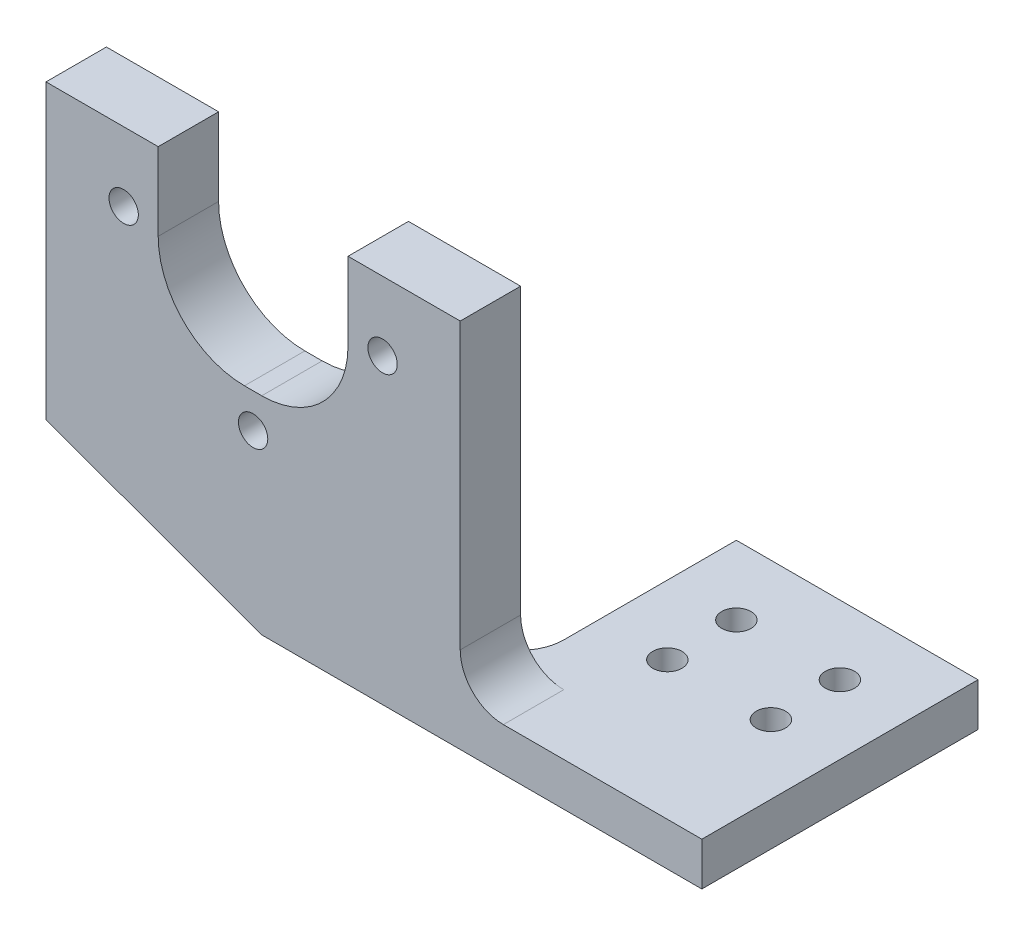
SolidWorks part; units mm, degrees
ref_plane "Front Plane" through (0, 0, 0) normal (0, 0, 1) x (1, 0, 0)
ref_plane "Top Plane" through (0, 0, 0) normal (0, 1, 0) x (1, 0, 0)
ref_plane "Right Plane" through (0, 0, 0) normal (1, 0, 0) x (0, 0, -1)
sketch "Sketch1" plane through (0, 0, 0) normal (0, 1, 0) x (1, 0, 0)
  line L1 (-14, -16) -> (14, -16)
  line L2 (-14, -16) -> (-14, 16)
  line L3 (-14, 16) -> (14, 16)
  line L4 (14, -16) -> (14, 16)
  line L5 (-14, -16) -> (14, 16) construction
  line L6 (-14, 16) -> (14, -16) construction
  point P0 (0, 0)
  dimension "D1" = 32
  dimension "D2" = 28
extrude "Boss-Extrude1" add sketch "Sketch1" along normal blind 5
hole_wizard "M3 Clearance Hole1" positions "Sketch3" profile "Sketch4" hole size "M3" standard "ANSI Metric" end condition through all
sketch "Sketch3" plane through (0, 5, 0) normal (0, 1, 0) x (1, 0, 0)
  line L0 (-14, 16) -> (-14, -16) construction
  line L2 (14, 16) -> (-14, 16) construction
  point P0 (-6, 8)
  point P2 (6, 8)
  point P4 (6, 0)
  point P6 (-6, 0)
  dimension "D1" = 8
  dimension "D2" = 12
  dimension "D3" = 8
  dimension "D4" = 8
sketch "Sketch4" plane through (-6, 5, -8) normal (1, 0, 0) x (0, 0, 1)
  line L0 (0, 0) -> (0, 5)
  line L1 (0, 5) -> (1.7, 5)
  line L2 (1.7, 5) -> (1.7, 0)
  line L5 (1.7, 0) -> (0, 0)
  line L11 (0, -6.35) -> (0, 107.95) construction
  dimension "Thru Hole Dia." = 3.4
  dimension "Thru Hole Depth" = 5
sketch "Sketch5" plane through (0, 0, 16) normal (0, 0, 1) x (1, 0, 0)
  line L0 (-14, 0) -> (-62, 0)
  line L1 (-62, 0) -> (-62, 43)
  line L2 (-62, 43) -> (-49, 43)
  line L3 (-49, 43) -> (-49, 24)
  line L4 (-49, 24) -> (-27, 24)
  line L5 (-27, 24) -> (-27, 43)
  line L6 (-27, 43) -> (-14, 43)
  line L9 (-14, 43) -> (-14, 0)
  line L11 (-38, 24) -> (-38, 0) construction
  dimension "D1" = 22
  dimension "D3" = 43
  dimension "D4" = 19
  dimension "D5" = 24
extrude "Boss-Extrude2" add sketch "Sketch5" against normal blind 7
fillet "Fillet1" radius 10 2 edges at (-27, 24, 12.5) (-49, 24, 12.5)
fillet "Fillet2" radius 5 1 edges at (-14, 5, 12.5)
fillet "Fillet3" radius 5 1 edges at (-14, 2.5, 9)
hole_wizard "M3 Clearance Hole2" positions "Sketch6" profile "Sketch7" hole size "M3" standard "ANSI Metric" end condition through all
sketch "Sketch6" plane through (0, 0, 16) normal (0, 0, 1) x (1, 0, 0)
  line L0 (-62, 0) -> (14, 0) construction
  line L1 (-38, 35) -> (-38, 20) construction
  line L3 (-37, 24) -> (-39, 24) construction
  circle A0 centre (-38, 35) radius 15 construction
  point P0 (-53, 35)
  point P2 (-23, 35)
  point P5 (-38, 20)
  point P29 (-38, 24)
  dimension "D1" = 30
  dimension "D2" = 35
sketch "Sketch7" plane through (-53, 35, 16) normal (1, 0, 0) x (0, -1, 0)
  line L0 (0, 0) -> (0, 32)
  line L1 (0, 32) -> (1.7, 32)
  line L2 (1.7, 32) -> (1.7, 0)
  line L5 (1.7, 0) -> (0, 0)
  line L11 (0, -6.35) -> (0, 107.95) construction
  dimension "Thru Hole Dia." = 3.4
  dimension "Thru Hole Depth" = 32
chamfer "Chamfer1" distance 25 angle 20 1 edges at (-62, 0, 12.5)
